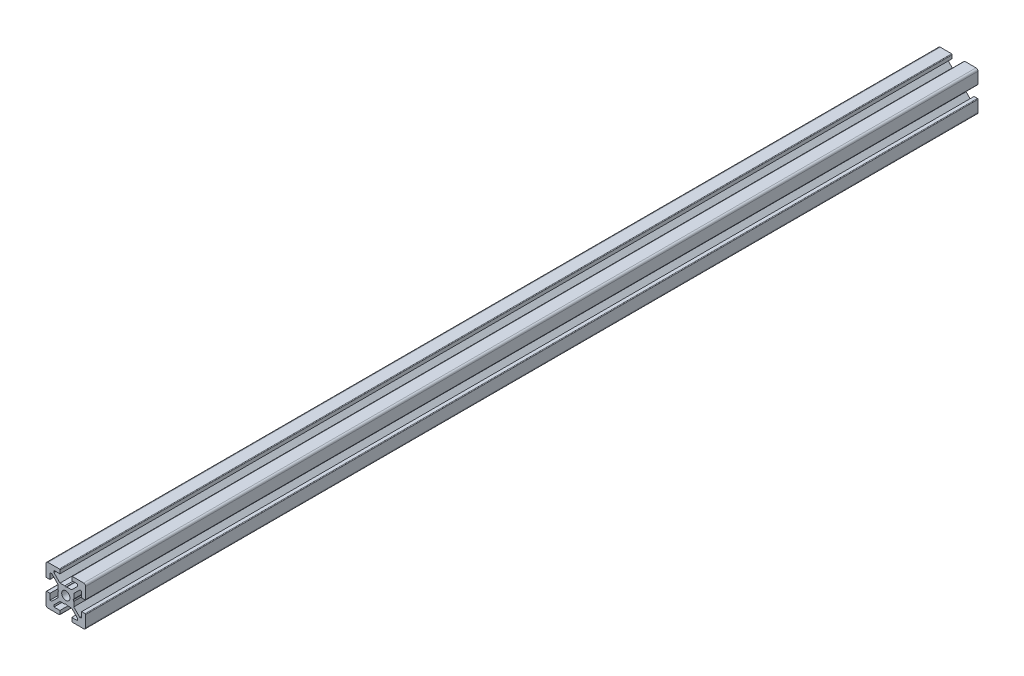
SolidWorks part; units mm, degrees
material "6061 Alloy"
ref_plane "Front Plane" through (0, 0, 0) normal (0, 0, 1) x (1, 0, 0)
ref_plane "Top Plane" through (0, 0, 0) normal (0, 1, 0) x (1, 0, 0)
ref_plane "Right Plane" through (0, 0, 0) normal (1, 0, 0) x (0, 0, -1)
sketch "Sketch1" plane through (0, 0, 0) normal (0, 0, -1) x (-1, 0, 0)
  line L0 (10, 3.3) -> (10, 9)
  line L1 (9, 10) -> (3.3, 10)
  line L2 (3, 9.7) -> (3, 8)
  line L3 (3, 8) -> (6, 8)
  line L4 (6, 8) -> (6, 7.0606)
  line L5 (6, 7.0606) -> (2.9394, 4)
  line L6 (2.9394, 4) -> (0.5196, 4)
  line L7 (0.5196, 4) -> (0, 3.7)
  line L8 (0, 3.7) -> (-0.5196, 4)
  line L9 (-0.5196, 4) -> (-2.9393, 4)
  line L10 (-2.9393, 4) -> (-6, 7.0607)
  line L11 (-6, 7.0607) -> (-6, 8)
  line L12 (-6, 8) -> (-3, 8)
  line L13 (-3, 8) -> (-3, 9.7)
  line L14 (-3.3, 10) -> (-9, 10)
  line L15 (-10, 9) -> (-10, 3.3)
  line L16 (-9.7, 3) -> (-8, 3)
  line L17 (-8, 3) -> (-8, 6)
  line L18 (-8, 6) -> (-7.0607, 6)
  line L19 (-7.0607, 6) -> (-4, 2.9393)
  line L20 (-4, 2.9393) -> (-4, 0.5196)
  line L21 (-4, 0.5196) -> (-3.7, 0)
  line L22 (-3.7, 0) -> (-4, -0.5196)
  line L23 (-4, -0.5196) -> (-4, -2.9393)
  line L24 (-4, -2.9393) -> (-7.0606, -6)
  line L25 (-7.0606, -6) -> (-8, -6)
  line L26 (-8, -6) -> (-8, -3)
  line L27 (-8, -3) -> (-9.7, -3)
  line L28 (-10, -3.3) -> (-10, -9)
  line L29 (-9, -10) -> (-3.3, -10)
  line L30 (-3, -9.7) -> (-3, -8)
  line L31 (-3, -8) -> (-6, -8)
  line L32 (-6, -8) -> (-6, -7.0607)
  line L33 (-6, -7.0607) -> (-2.9393, -4)
  line L34 (-2.9393, -4) -> (-0.5196, -4)
  line L35 (-0.5196, -4) -> (0, -3.7)
  line L36 (0, -3.7) -> (0.5196, -4)
  line L37 (0.5196, -4) -> (2.9393, -4)
  line L38 (2.9393, -4) -> (6, -7.0607)
  line L39 (6, -7.0607) -> (6, -8)
  line L40 (6, -8) -> (3, -8)
  line L41 (3, -8) -> (3, -9.7)
  line L42 (3.3, -10) -> (9, -10)
  line L43 (10, -9) -> (10, -3.3)
  line L44 (9.7, -3) -> (8, -3)
  line L45 (8, -3) -> (8, -6)
  line L46 (8, -6) -> (7.0607, -6)
  line L47 (7.0607, -6) -> (4, -2.9393)
  line L48 (4, -2.9393) -> (4, -0.5196)
  line L49 (4, -0.5196) -> (3.7, 0)
  line L50 (3.7, 0) -> (4, 0.5196)
  line L51 (4, 0.5196) -> (4, 2.9393)
  line L52 (4, 2.9393) -> (7.0607, 6)
  line L53 (7.0607, 6) -> (8, 6)
  line L54 (8, 6) -> (8, 3)
  line L55 (8, 3) -> (9.7, 3)
  arc A0 (10, 9) -> (9, 10) centre (9, 9) ccw
  arc A1 (3.3, 10) -> (3, 9.7) centre (3.3, 9.7) ccw
  arc A2 (-3, 9.7) -> (-3.3, 10) centre (-3.3, 9.7) ccw
  arc A3 (-9, 10) -> (-10, 9) centre (-9, 9) ccw
  arc A4 (-10, 3.3) -> (-9.7, 3) centre (-9.7, 3.3) ccw
  arc A5 (-9.7, -3) -> (-10, -3.3) centre (-9.7, -3.3) ccw
  arc A6 (-10, -9) -> (-9, -10) centre (-9, -9) ccw
  arc A7 (-3.3, -10) -> (-3, -9.7) centre (-3.3, -9.7) ccw
  arc A8 (3, -9.7) -> (3.3, -10) centre (3.3, -9.7) ccw
  arc A9 (9, -10) -> (10, -9) centre (9, -9) ccw
  arc A10 (10, -3.3) -> (9.7, -3) centre (9.7, -3.3) ccw
  arc A11 (9.7, 3) -> (10, 3.3) centre (9.7, 3.3) ccw
  circle A12 centre (0, 0) radius 2.1
extrude "Boss-Extrude1" add sketch "Sketch1" along normal blind 450
